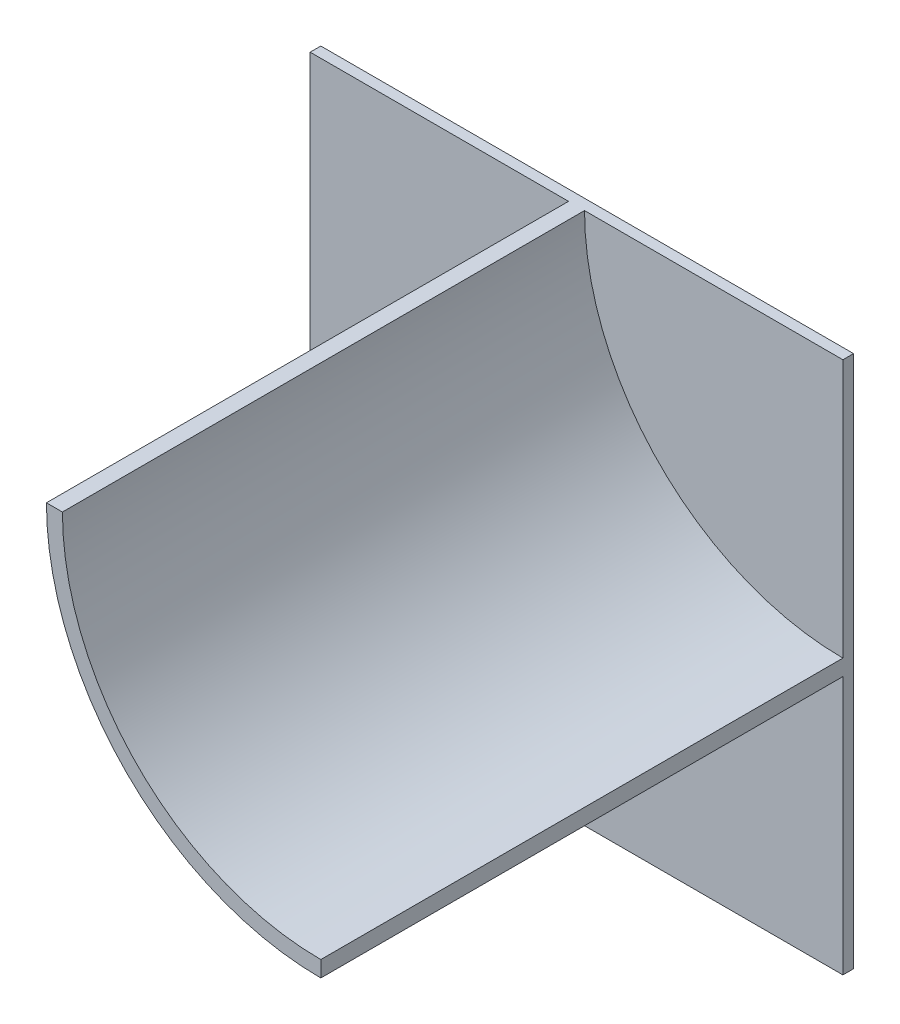
SolidWorks part; units mm, degrees
ref_plane "Płaszczyzna przednia" through (0, 0, 0) normal (0, 0, 1) x (1, 0, 0)
ref_plane "Płaszczyzna górna" through (0, 0, 0) normal (0, 1, 0) x (1, 0, 0)
ref_plane "Płaszczyzna prawa" through (0, 0, 0) normal (1, 0, 0) x (0, 0, -1)
sketch "Szkic1" plane through (0, 0, 0) normal (0, 0, 1) x (1, 0, 0)
  line L0 (0, 0) -> (100, 0)
  line L1 (0, 0) -> (-100, 0)
  line L2 (0, 0) -> (0, 100)
  line L3 (0, 0) -> (0, -100)
  line L4 (0, 100) -> (100, 100)
  line L5 (100, 100) -> (100, 0)
  line L6 (100, -100) -> (0, -100)
  line L7 (100, 0) -> (100, -100)
  line L8 (0, 100) -> (-100, 100)
  line L9 (-100, 100) -> (-100, 0)
  line L10 (-100, -100) -> (-100, 0)
  line L11 (0, -100) -> (-100, -100)
  dimension "D1" = 100
  dimension "D2" = 100
  dimension "D3" = 100
  dimension "D4" = 100
  dimension "D5" = 100
  dimension "D6" = 100
  dimension "D7" = 100
  dimension "D8" = 100
  dimension "D9" = 100
  dimension "D10" = 100
  dimension "D11" = 100
extrude "Dodanie-wyciągnięcie1" add sketch "Szkic1" along normal blind 4 contours L8 L9 L1 L2 | L5 L4 L2 L0 | L7 L0 L3 L6 | L11 L3 L1 L10
sketch "Szkic2" plane through (0, 0, 4) normal (0, 0, 1) x (1, 0, 0)
  line L2 (100, -100) -> (-100, -100) construction
  line L9 (-2, -100) -> (2, -100)
  line L20 (0, 0) -> (0, 100)
  line L23 (100, 100) -> (-100, 100) construction
  line L24 (0, 0) -> (100, 0)
  line L25 (100, 100) -> (100, -100) construction
  line L26 (100, 0) -> (100, 3)
  line L27 (100, 0) -> (100, -3)
  line L28 (0, 100) -> (3, 100)
  line L29 (0, 100) -> (-3, 100)
  circle A0 centre (100, 100) radius 97
  circle A1 centre (100, 100) radius 103
  line M10 (100, -100) -> (100, 100)
  line M11 (100, 100) -> (-100, 100)
  dimension "D1" = 3
  dimension "D2" = 3
  dimension "D3" = 3
  dimension "D4" = 3
  dimension "D8" = 4
extrude "Dodanie-wyciągnięcie5" add sketch "Szkic2" along normal blind 196 contours L20 A1 L24 A0 M10 M11 | L24 A1 M10 | A1 L20 M11
